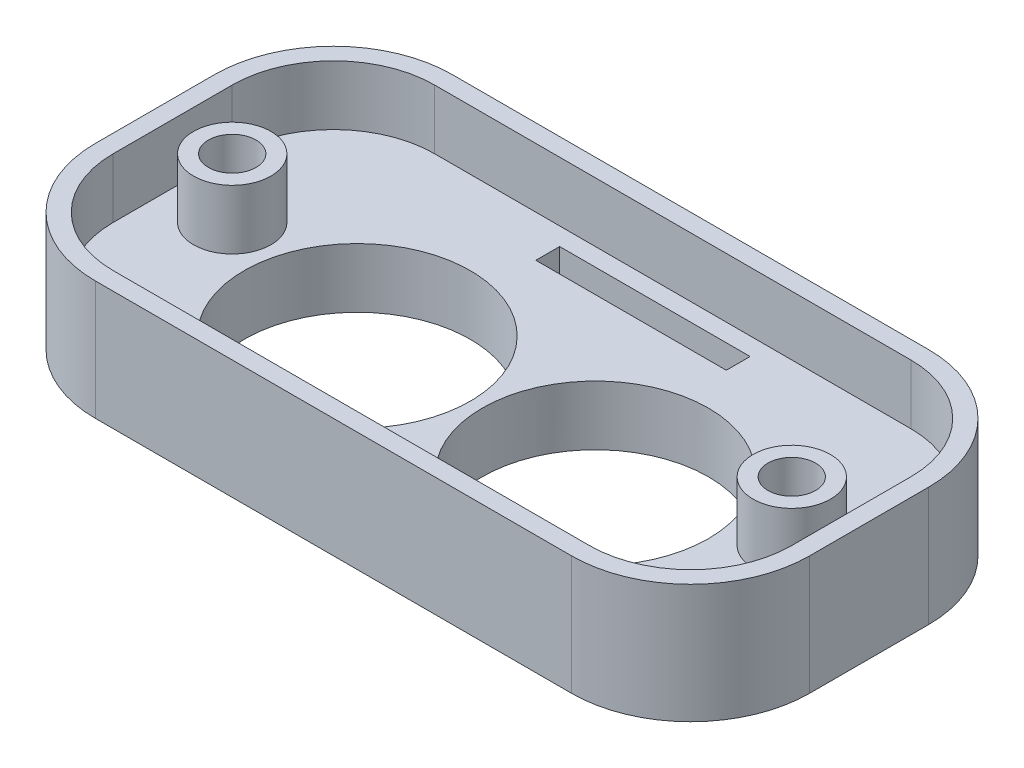
SolidWorks part; units mm, degrees
ref_plane "Спереди" through (0, 0, 0) normal (0, 0, 1) x (1, 0, 0)
ref_plane "Сверху" through (0, 0, 0) normal (0, 1, 0) x (1, 0, 0)
ref_plane "Справа" through (0, 0, 0) normal (1, 0, 0) x (0, 0, -1)
sketch "Эскиз1" plane through (0, 0, 0) normal (0, 1, 0) x (1, 0, 0)
  line L0 (-72.8908, 0) -> (73.0919, 0) construction
  line L1 (0, 46.6177) -> (0, -43.256) construction
  line L3 (-20, 18) -> (20, 18)
  line L4 (-30, 8) -> (-30, -2)
  line L5 (-20, -12) -> (20, -12)
  line L6 (30, 8) -> (30, -2)
  circle A0 centre (-10, 0) radius 9.5
  circle A1 centre (10, 0) radius 9.5
  arc A2 (20, 18) -> (30, 8) centre (20, 8) cw
  arc A3 (20, -12) -> (30, -2) centre (20, -2) ccw
  arc A4 (-30, -2) -> (-20, -12) centre (-20, -2) ccw
  arc A5 (-20, 18) -> (-30, 8) centre (-20, 8) ccw
  point P19 (-30, -12)
  point P22 (-30, 18)
  dimension "D1" = 19
  dimension "D2" = 10
  dimension "D3" = 18
  dimension "D7" = 10
  dimension "D4" = 30
  dimension "D5" = 30
  dimension "D6" = 30
extrude "Бобышка-Вытянуть1" add sketch "Эскиз1" along normal blind 10
sketch "Эскиз2" plane through (0, 10, 0) normal (0, 1, 0) x (1, 0, 0)
  line L0 (-20, -12) -> (20, -12) construction
  line L1 (30, -2) -> (30, 8) construction
  line L2 (20, 18) -> (-20, 18) construction
  line L3 (-20, -12) -> (20, -12)
  line L4 (30, -2) -> (30, 8)
  line L5 (20, 18) -> (-20, 18)
  line L6 (-30, 8) -> (-30, -2) construction
  line L7 (-30, 8) -> (-30, -2)
  line L8 (-20, 16.5) -> (20, 16.5)
  line L9 (-20, -10.5) -> (20, -10.5)
  line L10 (-20, 16.5) -> (-20, -10.5) construction
  line L11 (-28.5, 8) -> (-28.5, -2)
  line L12 (0, 19.9133) -> (0, -21.3858) construction
  line L13 (28.5, 8) -> (28.5, -2)
  arc A0 (-30, -2) -> (-20, -12) centre (-20, -2) ccw construction
  arc A1 (20, -12) -> (30, -2) centre (20, -2) ccw construction
  arc A2 (30, 8) -> (20, 18) centre (20, 8) ccw construction
  arc A3 (-20, 18) -> (-30, 8) centre (-20, 8) ccw construction
  arc A4 (-30, -2) -> (-20, -12) centre (-20, -2) ccw
  arc A5 (20, -12) -> (30, -2) centre (20, -2) ccw
  arc A6 (30, 8) -> (20, 18) centre (20, 8) ccw
  arc A7 (-20, 18) -> (-30, 8) centre (-20, 8) ccw
  circle A8 centre (-20, 8) radius 8.5
  circle A9 centre (-20, -2) radius 8.5
  circle A10 centre (20, 8) radius 8.5
  circle A11 centre (20, -2) radius 8.5
  point P24 (0, 16.5)
  point P29 (0, -10.5)
  circle M13 centre (-10, 0) radius 9.5
  circle M14 centre (10, 0) radius 9.5
  dimension "D1" = 1.5
  dimension "D2" = 1.5
extrude "Вырез-Вытянуть1" cut sketch "Эскиз2" against normal blind 5 contours A9 A8 M13 | L9 A11 A10 L8 A8 A9 M14 M13 | A9 A8 M13 | A9 A8 M13 | A9 A8 L11 | A11 A10 M14 | A11 A10 M14 | A11 A10 M14 | A10 A11 L13
sketch "Эскиз3" plane through (0, 5, 0) normal (0, 1, 0) x (1, 0, 0)
  line L0 (-28.5, 3) -> (28.9714, 3) construction
  line L1 (-30, 8) -> (-30, -2) construction
  line L2 (0, 16.5) -> (0, -10.5) construction
  line L3 (-20, 16.5) -> (20, 16.5) construction
  line L4 (-20, -10.5) -> (20, -10.5) construction
  line L5 (-28.5, 8) -> (-28.5, -2) construction
  circle A0 centre (-23.5, 3) radius 3.25
  circle A1 centre (-23.5, 3) radius 2
  circle A2 centre (23.5, 3) radius 3.25
  circle A3 centre (23.5, 3) radius 2
  dimension "D1" = 6.5
  dimension "D2" = 6.5
  dimension "D3" = 4
extrude "Бобышка-Вытянуть2" add sketch "Эскиз3" along normal blind 5
sketch "Эскиз4" plane through (0, 5, 0) normal (0, 1, 0) x (1, 0, 0)
  line L0 (0, 16.5) -> (0, -10.5) construction
  line L1 (-8, 15) -> (8, 15)
  line L2 (-8, 15) -> (-8, 13)
  line L3 (-8, 13) -> (8, 13)
  line L4 (8, 15) -> (8, 13)
  line L5 (-20, 16.5) -> (20, 16.5) construction
  line L6 (-20, -10.5) -> (20, -10.5) construction
  line L7 (-28.5, 3) -> (28.5, 3) construction
  line L8 (-28.5, 8) -> (-28.5, -2) construction
  line L9 (28.5, 8) -> (28.5, -2) construction
  point P10 (0, 13)
  dimension "D1" = 2
  dimension "D2" = 8
  dimension "D3" = 1.5
extrude "Вырез-Вытянуть2" cut sketch "Эскиз4" against normal through all
sketch "Эскиз5" plane through (0, 10, 0) normal (0, 1, 0) x (1, 0, 0)
  line L4 (-30, 8) -> (-30, -2) construction
  line L5 (-28.5, 8) -> (-28.5, -2) construction
  line L6 (-20, -12) -> (20, -12) construction
  line L7 (-20, -10.5) -> (20, -10.5) construction
  line L8 (30, -2) -> (30, 8) construction
  line L9 (28.5, 8) -> (28.5, -2) construction
  line L10 (20, 18) -> (-20, 18) construction
  line L11 (-20, 16.5) -> (20, 16.5) construction
  line L12 (-30, 8) -> (-30, -2)
  line L13 (-28.5, 8) -> (-28.5, -2)
  line L14 (-20, -12) -> (20, -12)
  line L15 (-20, -10.5) -> (20, -10.5)
  line L16 (30, -2) -> (30, 8)
  line L17 (28.5, 8) -> (28.5, -2)
  line L18 (20, 18) -> (-20, 18)
  line L19 (-20, 16.5) -> (20, 16.5)
  arc A0 (-30, -2) -> (-20, -12) centre (-20, -2) ccw construction
  arc A2 (-20, 18) -> (-30, 8) centre (-20, 8) ccw construction
  arc A4 (-20, 18) -> (-30, 8) centre (-20, 8) ccw
  arc A5 (-28.5, -2) -> (-20, -10.5) centre (-20, -2) ccw construction
  arc A6 (20, -12) -> (30, -2) centre (20, -2) ccw construction
  arc A7 (20, -10.5) -> (28.5, -2) centre (20, -2) ccw construction
  arc A8 (28.5, 8) -> (20, 16.5) centre (20, 8) ccw construction
  arc A9 (30, 8) -> (20, 18) centre (20, 8) ccw construction
  arc A10 (-20, 16.5) -> (-28.5, 8) centre (-20, 8) ccw construction
  arc A11 (-30, -2) -> (-20, -12) centre (-20, -2) ccw
  arc A12 (-28.5, -2) -> (-20, -10.5) centre (-20, -2) ccw
  arc A13 (20, -12) -> (30, -2) centre (20, -2) ccw
  arc A14 (20, -10.5) -> (28.5, -2) centre (20, -2) ccw
  arc A15 (28.5, 8) -> (20, 16.5) centre (20, 8) ccw
  arc A16 (30, 8) -> (20, 18) centre (20, 8) ccw
  arc A17 (-20, 16.5) -> (-28.5, 8) centre (-20, 8) ccw
